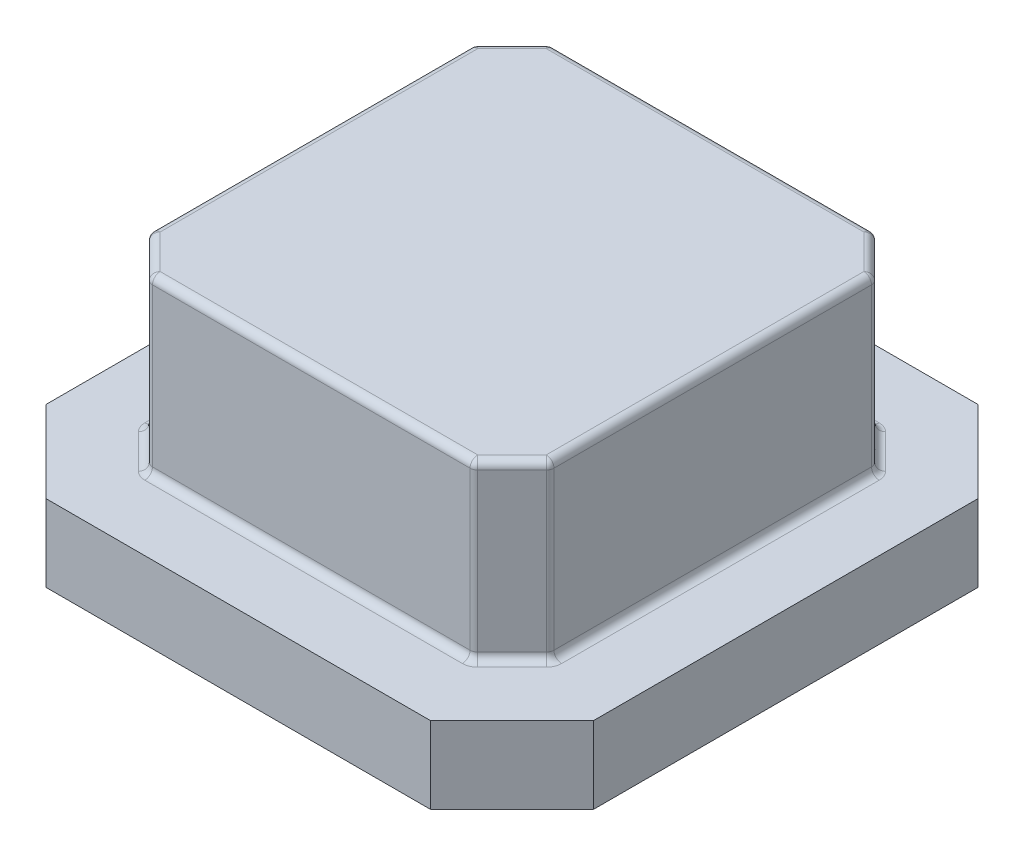
SolidWorks part; units mm, degrees
material "PVC 0.007 Plasticized"
ref_plane "Front Plane" through (0, 0, 0) normal (0, 0, 1) x (1, 0, 0)
ref_plane "Top Plane" through (0, 0, 0) normal (0, 1, 0) x (1, 0, 0)
ref_plane "Right Plane" through (0, 0, 0) normal (1, 0, 0) x (0, 0, -1)
sketch "Sketch2" plane through (0, 0, 0) normal (0, 1, 0) x (1, 0, 0)
  line L0 (-56.6615, 0) -> (70.3385, 0)
  line L1 (70.3385, 0) -> (97.2792, 26.9408)
  line L2 (97.2792, 26.9408) -> (97.2792, 153.9408)
  line L3 (-56.6615, 0) -> (-83.6023, 26.9408)
  line L4 (-83.6023, 26.9408) -> (-83.6023, 153.9408)
  line L5 (-83.6023, 153.9408) -> (-56.6615, 180.8815)
  line L7 (70.3385, 180.8815) -> (97.2792, 153.9408)
  line L10 (70.3385, 180.8815) -> (-56.6615, 180.8815)
  point P9 (0, 0)
  point P10 (0, 0)
  dimension "D1" = 127
  dimension "D2" = 127
  dimension "D3" = 38.1
  dimension "D4" = 135
  dimension "D5" = 135
  dimension "D6" = 38.1
  dimension "D7" = 135
  dimension "D8" = 135
  dimension "D9" = 127
  dimension "D10" = 127
extrude "Boss-Extrude1" add sketch "Sketch2" along normal blind 25.4
sketch "Sketch3" plane through (0, 25.4, 0) normal (0, 1, 0) x (1, 0, 0)
  line L44 (-59.4723, 36.9357) -> (-46.6666, 24.13)
  line L45 (-46.6666, 24.13) -> (60.3435, 24.13)
  line L46 (60.3435, 24.13) -> (73.1492, 36.9357)
  line L47 (73.1492, 36.9357) -> (73.1492, 143.9458)
  line L48 (73.1492, 143.9458) -> (60.3435, 156.7515)
  line L49 (60.3435, 156.7515) -> (-46.6666, 156.7515)
  line L50 (-46.6666, 156.7515) -> (-59.4723, 143.9458)
  line L51 (-59.4723, 143.9458) -> (-59.4723, 36.9357)
  line L52 (-59.4723, 36.9357) -> (-46.6666, 24.13)
  line L53 (-46.6666, 24.13) -> (60.3435, 24.13)
  line L54 (60.3435, 24.13) -> (73.1492, 36.9357)
  line L55 (73.1492, 36.9357) -> (73.1492, 143.9458)
  line L56 (73.1492, 143.9458) -> (60.3435, 156.7515)
  line L57 (60.3435, 156.7515) -> (-46.6666, 156.7515)
  line L58 (-46.6666, 156.7515) -> (-59.4723, 143.9458)
  line L59 (-59.4723, 143.9458) -> (-59.4723, 36.9357)
  dimension "D1" = 24.13
extrude "Boss-Extrude2" add sketch "Sketch3" along normal blind 57.15
fillet "Fillet1" radius 2.54 24 edges at (66.7464, 25.4, -30.5329) (73.1492, 53.975, -36.9357) (73.1492, 25.4, -90.4408) (73.1492, 53.975, -143.9458) (66.7464, 25.4, -150.3487) (60.3435, 53.975, -156.7515) (6.8385, 25.4, -156.7515) (-46.6666, 53.975, -156.7515) (-53.0694, 25.4, -150.3487) (-59.4723, 53.975, -143.9458) (-59.4723, 25.4, -90.4408) (60.3435, 53.975, -24.13) (6.8385, 25.4, -24.13) (-59.4723, 53.975, -36.9357) (-46.6666, 53.975, -24.13) (-53.0694, 25.4, -30.5329) (-53.0694, 82.55, -150.3487) (6.8385, 82.55, -156.7515) (66.7464, 82.55, -150.3487) (73.1492, 82.55, -90.4408) (66.7464, 82.55, -30.5329) (6.8385, 82.55, -24.13) (-53.0694, 82.55, -30.5329) (-59.4723, 82.55, -90.4408)
